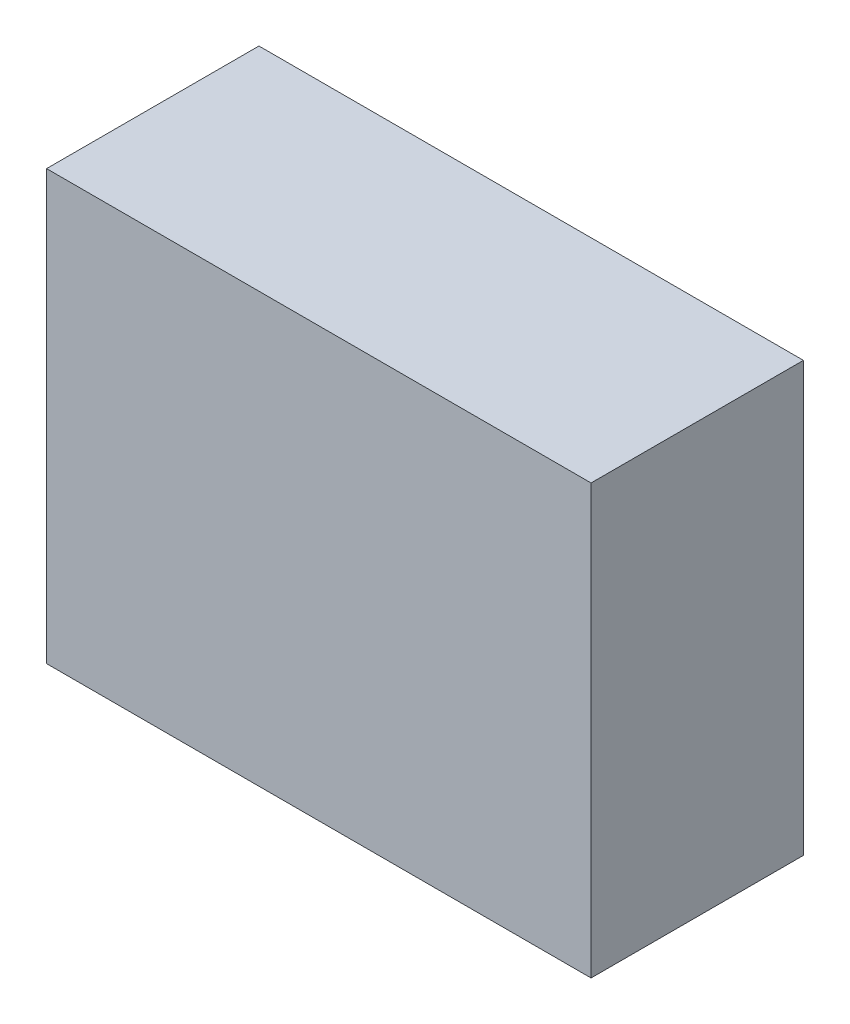
SolidWorks part; units mm, degrees
material "Copper"
ref_plane "Front Plane" through (0, 0, 0) normal (0, 0, 1) x (1, 0, 0)
ref_plane "Top Plane" through (0, 0, 0) normal (0, 1, 0) x (1, 0, 0)
ref_plane "Right Plane" through (0, 0, 0) normal (1, 0, 0) x (0, 0, -1)
sketch "Sketch1" plane through (0, 0, 0) normal (0, 0, 1) x (1, 0, 0)
  line L1 (-15.875, -12.5) -> (15.875, -12.5)
  line L2 (-15.875, -12.5) -> (-15.875, 12.5)
  line L3 (-15.875, 12.5) -> (15.875, 12.5)
  line L4 (15.875, -12.5) -> (15.875, 12.5)
  line L5 (-15.875, -12.5) -> (15.875, 12.5) construction
  line L6 (-15.875, 12.5) -> (15.875, -12.5) construction
  point P0 (0, 0)
  dimension "D1" = 31.75
  dimension "D2" = 25
extrude "Boss-Extrude1" add sketch "Sketch1" along normal blind 12.3826
